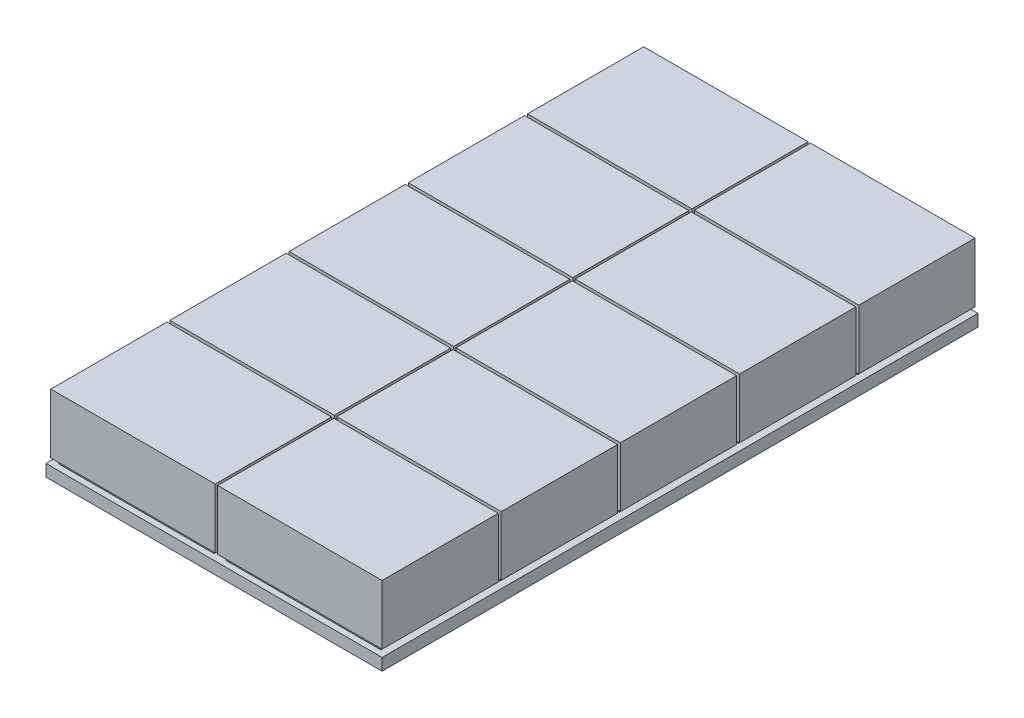
SolidWorks part; units mm, degrees
ref_plane "Front Plane" through (0, 0, 0) normal (0, 0, 1) x (1, 0, 0)
ref_plane "Top Plane" through (0, 0, 0) normal (0, 1, 0) x (1, 0, 0)
ref_plane "Right Plane" through (0, 0, 0) normal (1, 0, 0) x (0, 0, -1)
sketch "Sketch1" plane through (0, 0, 0) normal (0, 1, 0) x (1, 0, 0)
  line L1 (-35.5, -125) -> (35.5, -125)
  line L2 (-35.5, -125) -> (-35.5, 125)
  line L3 (-35.5, 125) -> (35.5, 125)
  line L4 (35.5, -125) -> (35.5, 125)
  line L5 (-35.5, -125) -> (35.5, 125) construction
  line L6 (-35.5, 125) -> (35.5, -125) construction
  point P0 (0, 0)
  dimension "D1" = 71
  dimension "D2" = 250
extrude "Boss-Extrude1" add sketch "Sketch1" along normal blind 5
sketch "Sketch2" plane through (0, 5, 0) normal (0, 1, 0) x (1, 0, 0)
  line L0 (0, 0) -> (0, -125) construction
  line L1 (-35.5, -125) -> (35.5, -125) construction
  line L3 (-32.5, -77.5) -> (32.5, -77.5)
  line L4 (-32.5, -77.5) -> (-32.5, -122.5)
  line L5 (-32.5, -122.5) -> (32.5, -122.5)
  line L6 (32.5, -77.5) -> (32.5, -122.5)
  line L7 (-32.5, -77.5) -> (32.5, -122.5) construction
  line L8 (-32.5, -122.5) -> (32.5, -77.5) construction
  point P5 (0, -100)
  dimension "D1" = 65
  dimension "D2" = 45
  dimension "D3" = 2.5
extrude "Boss-Extrude3" add sketch "Sketch2" along normal blind 2
pattern_linear "LPattern1" count 5 spacing 50 along (0, 0, -1) of "Boss-Extrude3"
sketch "Sketch3" plane through (0, 7, 0) normal (0, 1, 0) x (1, 0, 0)
  line L0 (0, 0) -> (0, -122.5) construction
  line L1 (-32.5, -122.5) -> (32.5, -122.5) construction
  line L2 (-35.5, 125) -> (-35.5, -125) construction
  line L3 (-34.5, -75.2576) -> (34.5, -75.2576)
  line L4 (-34.5, -75.2576) -> (-34.5, -124.0124)
  line L5 (-34.5, -124.0124) -> (34.5, -124.0124)
  line L6 (34.5, -75.2576) -> (34.5, -124.0124)
  line L7 (-34.5, -75.2576) -> (34.5, -124.0124) construction
  line L8 (-34.5, -124.0124) -> (34.5, -75.2576) construction
  point P5 (0, -99.635)
  dimension "D1" = 1
extrude "Boss-Extrude8" add sketch "Sketch3" along normal blind 25
pattern_linear "LPattern5" count 5 spacing 50 along (0, 0, -1) of "Boss-Extrude8"
sketch "Sketch5" plane through (0, 0, 0) normal (0, 1, 0) x (1, 0, 0)
  line L0 (0, 0) -> (208.2024, 0) construction
pattern_linear "LPattern6" count 2 spacing 70 along (1, 0, 0) of "Boss-Extrude1", "Boss-Extrude3", "LPattern1", "Boss-Extrude8", "LPattern5"
